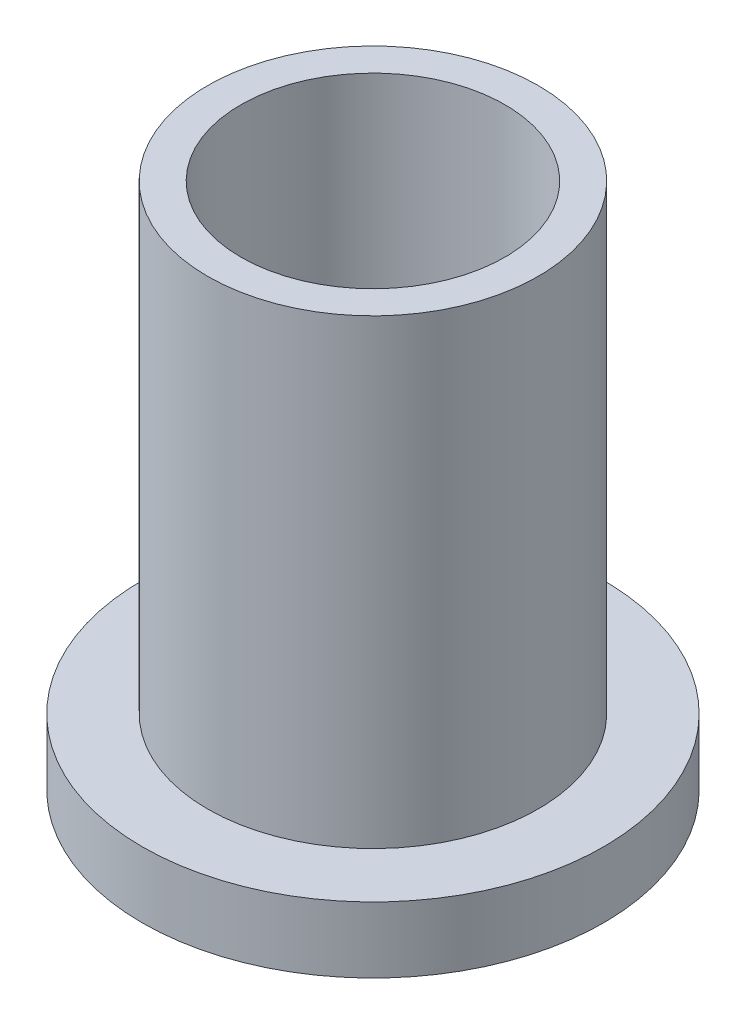
SolidWorks part; units mm, degrees
ref_plane "Front" through (0, 0, 0) normal (0, 0, 1) x (1, 0, 0)
ref_plane "Top" through (0, 0, 0) normal (0, 1, 0) x (1, 0, 0)
ref_plane "Right" through (0, 0, 0) normal (1, 0, 0) x (0, 0, -1)
sketch "Sketch1" plane through (0, 0, 0) normal (0, 1, 0) x (1, 0, 0)
  circle A0 centre (0, 0) radius 6.3627
  circle A1 centre (0, 0) radius 7.9629
  circle A2 centre (0, 0) radius 11.1125
  dimension "ID" = 12.7254
  dimension "OD" = 15.9258
  dimension "FlangeOD" = 22.225
sketch "Sketch2" plane through (0, 0, 0) normal (0, 1, 0) x (1, 0, 0)
  circle A0 centre (0, 0) radius 6.3627 construction
  circle A1 centre (0, 0) radius 7.9629 construction
  circle A2 centre (0, 0) radius 6.3627
  circle A3 centre (0, 0) radius 7.9629
extrude "Boss-Extrude1" add sketch "Sketch2" along normal blind 25.4
sketch "Sketch3" plane through (0, 0, 0) normal (0, 1, 0) x (1, 0, 0)
  circle A0 centre (0, 0) radius 11.1125 construction
  circle A1 centre (0, 0) radius 7.9629 construction
  circle A2 centre (0, 0) radius 11.1125
  circle A3 centre (0, 0) radius 7.9629
extrude "Boss-Extrude2" add sketch "Sketch3" along normal blind 3.175
